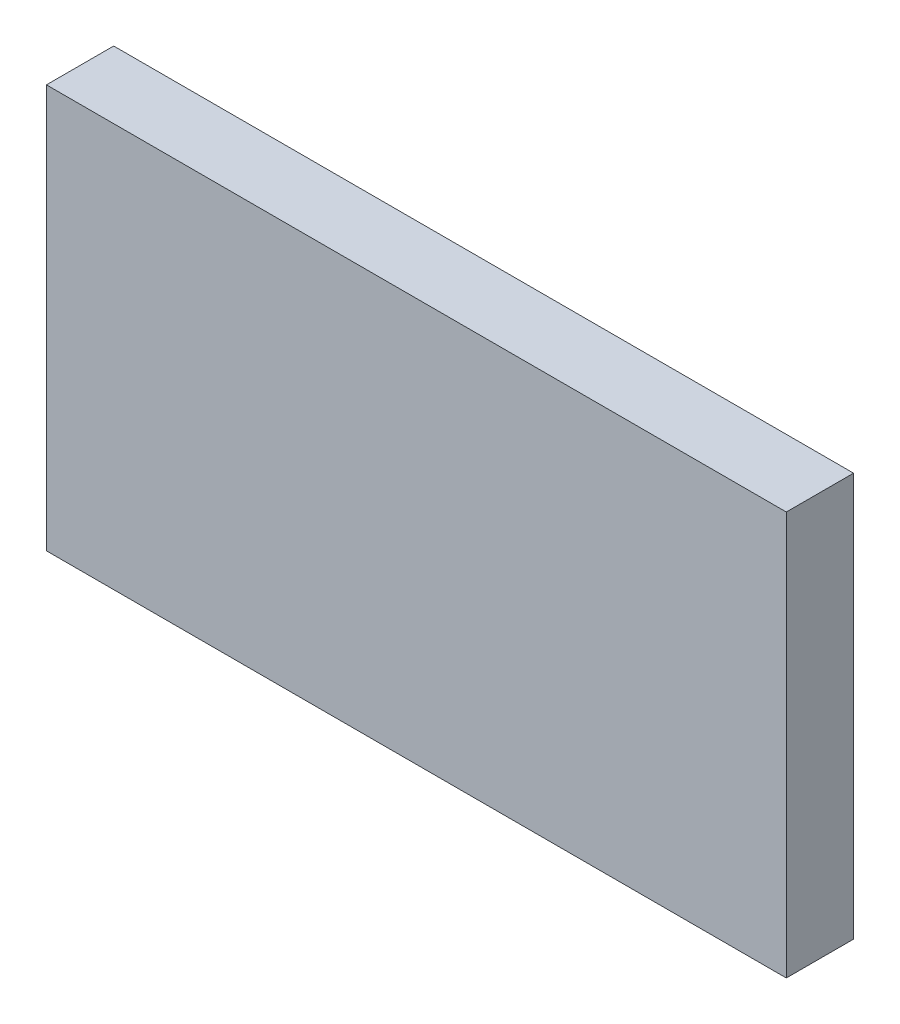
SolidWorks part; units mm, degrees
ref_plane "Front Plane" through (0, 0, 0) normal (0, 0, 1) x (1, 0, 0)
ref_plane "Top Plane" through (0, 0, 0) normal (0, 1, 0) x (1, 0, 0)
ref_plane "Right Plane" through (0, 0, 0) normal (1, 0, 0) x (0, 0, -1)
sketch "Sketch2" plane through (0, 0, 0) normal (0, 0, 1) x (1, 0, 0)
  line L1 (0, 0) -> (33, 0)
  line L2 (0, 0) -> (0, 18)
  line L3 (0, 18) -> (33, 18)
  line L4 (33, 0) -> (33, 18)
  dimension "D1" = 33
  dimension "D2" = 18
extrude "Boss-Extrude1" add sketch "Sketch2" along normal blind 3
